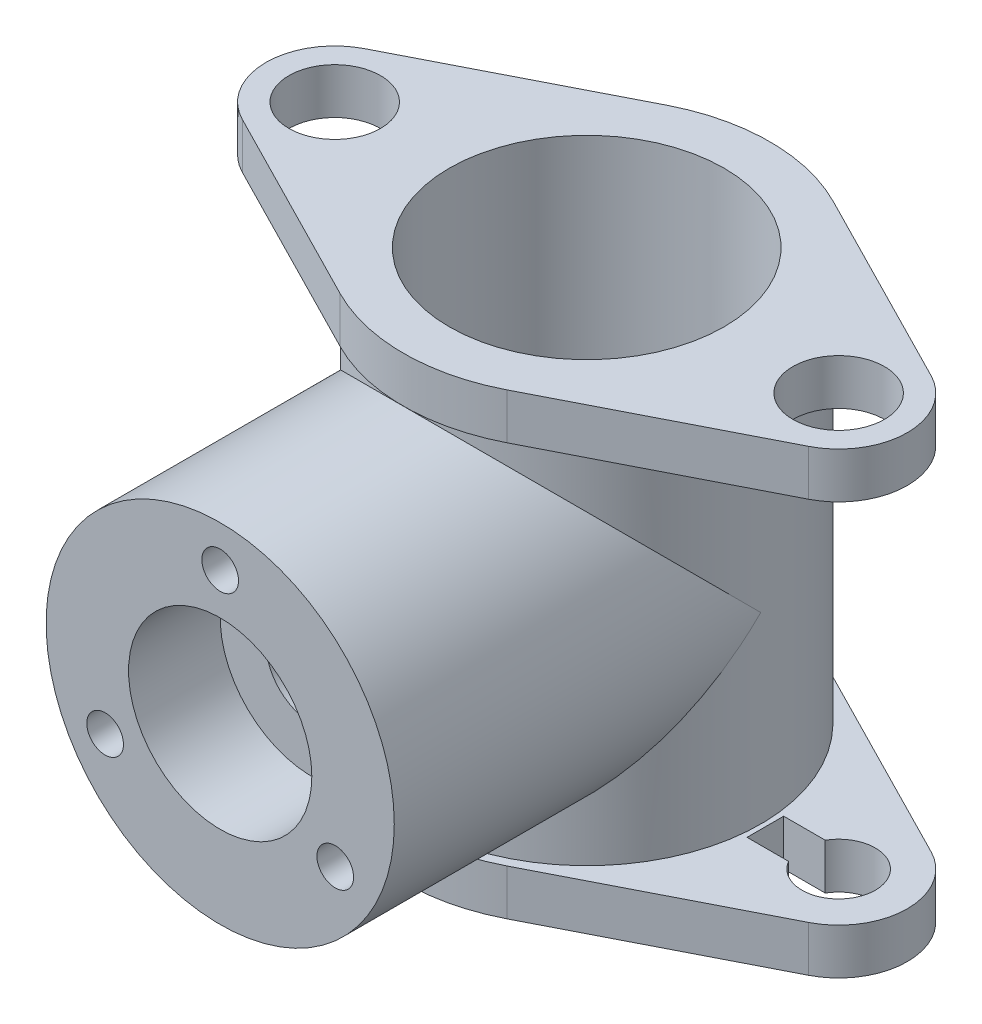
SolidWorks part; units mm, degrees
ref_plane "Front Plane" through (0, 0, 0) normal (0, 0, 1) x (1, 0, 0)
ref_plane "Top Plane" through (0, 0, 0) normal (0, 1, 0) x (1, 0, 0)
ref_plane "Right Plane" through (0, 0, 0) normal (1, 0, 0) x (0, 0, -1)
sketch "Sketch1" plane through (0, 0, 0) normal (0, 1, 0) x (1, 0, 0)
  line L0 (0, 0) -> (-43.4179, 0) construction
  line L1 (0, 0) -> (0, 20) construction
  line L2 (-9.0909, 17.8145) -> (-30.9091, 6.6804)
  line L3 (-9.0909, -17.8145) -> (-30.9091, -6.6804)
  line L4 (9.0909, -17.8145) -> (30.9091, -6.6804)
  line L5 (9.0909, 17.8145) -> (30.9091, 6.6804)
  line L6 (-23.5, 2) -> (-24.0359, 2)
  line L7 (-19.5, -2) -> (-23.5, -2)
  line L8 (-19.5, -2) -> (-19.5, 2)
  line L9 (-19.5, 2) -> (-23.5, 2)
  line L11 (23.5, 2) -> (24.0359, 2)
  line L12 (19.5, 2) -> (23.5, 2)
  line L13 (19.5, -2) -> (19.5, 2)
  line L14 (-24.0359, -2) -> (-23.5, -2)
  line L15 (19.5, -2) -> (23.5, -2)
  line L16 (24.0359, -2) -> (23.5, -2)
  arc A0 (-9.0909, -17.8145) -> (9.0909, -17.8145) centre (0, 0) ccw
  arc A1 (-30.9091, 6.6804) -> (-30.9091, -6.6804) centre (-27.5, 0) ccw
  arc A2 (30.9091, 6.6804) -> (30.9091, -6.6804) centre (27.5, 0) cw
  arc A3 (9.0909, 17.8145) -> (-9.0909, 17.8145) centre (0, 0) ccw
  circle A4 centre (0, 0) radius 15
  arc A5 (-24.0359, 2) -> (-24.0359, -2) centre (-27.5, 0) ccw
  arc A6 (24.0359, 2) -> (24.0359, -2) centre (27.5, 0) cw
  point P16 (-21.5, 0)
  dimension "D1" = 15
  dimension "D2" = 40
  dimension "D3" = 4
  dimension "D5" = 8
  dimension "D4" = 4
extrude "Boss-Extrude1" add sketch "Sketch1" along normal blind 5
sketch "Sketch2" plane through (0, 5, 0) normal (0, 1, 0) x (1, 0, 0)
  circle A0 centre (0, 0) radius 15
  circle A1 centre (0, 0) radius 19
extrude "Boss-Extrude2" add sketch "Sketch2" along normal blind 40
sketch "Sketch3" plane through (0, 45, 0) normal (0, 1, 0) x (1, 0, 0)
  line L4 (9.0909, -17.8145) -> (30.9091, -6.6804)
  line L5 (30.9091, 6.6804) -> (9.0909, 17.8145)
  line L6 (-9.0909, 17.8145) -> (-30.9091, 6.6804)
  line L7 (-30.9091, -6.6804) -> (-9.0909, -17.8145)
  line L8 (9.0909, -17.8145) -> (30.9091, -6.6804)
  line L9 (30.9091, 6.6804) -> (9.0909, 17.8145)
  line L10 (-9.0909, 17.8145) -> (-30.9091, 6.6804)
  line L11 (-30.9091, -6.6804) -> (-9.0909, -17.8145)
  circle A0 centre (-27.5, 0) radius 5
  circle A1 centre (27.5, 0) radius 5
  circle A2 centre (0, 0) radius 15
  arc A4 (-9.0909, -17.8145) -> (9.0909, -17.8145) centre (0, 0) ccw
  arc A5 (30.9091, -6.6804) -> (30.9091, 6.6804) centre (27.5, 0) ccw
  arc A6 (9.0909, 17.8145) -> (-9.0909, 17.8145) centre (0, 0) ccw
  arc A7 (-30.9091, 6.6804) -> (-30.9091, -6.6804) centre (-27.5, 0) ccw
  arc A8 (-9.0909, -17.8145) -> (9.0909, -17.8145) centre (0, 0) ccw
  arc A9 (30.9091, -6.6804) -> (30.9091, 6.6804) centre (27.5, 0) ccw
  arc A10 (9.0909, 17.8145) -> (-9.0909, 17.8145) centre (0, 0) ccw
  arc A11 (-30.9091, 6.6804) -> (-30.9091, -6.6804) centre (-27.5, 0) ccw
  dimension "D1" = 0
extrude "Boss-Extrude4" add sketch "Sketch3" along normal blind 5
ref_plane "Plane1" through (0, 0, 40) normal (0, 0, 1) x (1, 0, 0)
sketch "Sketch4" plane through (0, 0, 40) normal (0, 0, 1) x (1, 0, 0)
  line L0 (0, 0) -> (0, 50) construction
  line L1 (9.0909, 50) -> (-9.0909, 50) construction
  circle A0 centre (0, 25) radius 19
extrude "Boss-Extrude5" add sketch "Sketch4" against normal up to surface (40 mm away)
sketch "Sketch5" plane through (0, 0, 40) normal (0, 0, 1) x (1, 0, 0)
  circle A0 centre (0, 25) radius 10
extrude "Cut-Extrude1" cut sketch "Sketch5" against normal blind 10
sketch "Sketch6" plane through (0, 0, 30) normal (0, 0, 1) x (1, 0, 0)
  circle A0 centre (0, 25) radius 5
extrude "Cut-Extrude2" cut sketch "Sketch6" against normal blind 48
ref_plane "Plane2" through (0, 0, -20) normal (0, 0, 1) x (1, 0, 0)
sketch "Sketch7" plane through (0, 0, -20) normal (0, 0, 1) x (1, 0, 0)
  line L0 (0, 0) -> (0, 50) construction
  line L1 (9.0909, 50) -> (-9.0909, 50) construction
  circle A0 centre (0, 25) radius 6
extrude "Boss-Extrude6" add sketch "Sketch7" along normal up to surface (1.9722 mm away)
sketch "Sketch8" plane through (0, 0, 40) normal (0, 0, 1) x (1, 0, 0)
  circle A0 centre (0, 25) radius 14.5 construction
  circle A1 centre (0, 39.5) radius 2
  circle A2 centre (12.5574, 17.75) radius 2
  circle A3 centre (-12.5574, 17.75) radius 2
  point P12 (0, 25)
  dimension "D1" = 3
extrude "Cut-Extrude3" cut sketch "Sketch8" against normal blind 15
